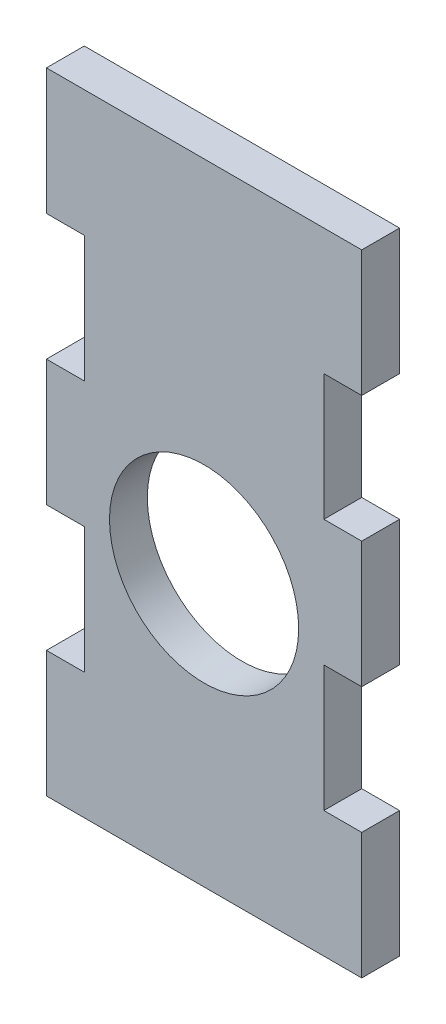
SolidWorks part; units mm, degrees
material "PC High Viscosity"
ref_plane "Front Plane" through (0, 0, 0) normal (0, 0, 1) x (1, 0, 0)
ref_plane "Top Plane" through (0, 0, 0) normal (0, 1, 0) x (1, 0, 0)
ref_plane "Right Plane" through (0, 0, 0) normal (1, 0, 0) x (0, 0, -1)
sketch "Sketch1" plane through (0, 0, 0) normal (0, 0, 1) x (1, 0, 0)
  line L1 (12.5, -25) -> (-12.5, -25)
  line L2 (12.5, -25) -> (12.5, 25)
  line L3 (12.5, 25) -> (-12.5, 25)
  line L4 (-12.5, -25) -> (-12.5, 25)
  line L5 (12.5, -25) -> (-12.5, 25) construction
  line L6 (12.5, 25) -> (-12.5, -25) construction
  point P0 (0, 0)
  dimension "D1" = 25
  dimension "D2" = 50
extrude "Boss-Extrude1" add sketch "Sketch1" along normal blind 3
sketch "Sketch2" plane through (0, 0, 3) normal (0, 0, 1) x (1, 0, 0)
  line L0 (12.5, -25) -> (12.5, 25) construction
  line L1 (12.5, 15) -> (9.5, 15)
  line L2 (12.5, 15) -> (12.5, 5)
  line L3 (12.5, 5) -> (9.5, 5)
  line L4 (9.5, 15) -> (9.5, 5)
  line L5 (0, 25) -> (0, -25) construction
  line L6 (12.5, -5) -> (9.5, -5)
  line L7 (12.5, -5) -> (12.5, -15)
  line L8 (12.5, -15) -> (9.5, -15)
  line L9 (9.5, -5) -> (9.5, -15)
  line L10 (12.5, 25) -> (-12.5, 25) construction
  line L11 (-12.5, -25) -> (12.5, -25) construction
  line L12 (12.5, 0) -> (-12.5, 0) construction
  line L13 (-12.5, 25) -> (-12.5, -25) construction
  line L14 (12.5, 5) -> (12.5, -5) construction
  line L15 (-9.5, -5) -> (-9.5, -15)
  line L16 (-12.5, -15) -> (-9.5, -15)
  line L17 (-12.5, -5) -> (-12.5, -15)
  line L18 (-12.5, -5) -> (-9.5, -5)
  line L19 (-9.5, 15) -> (-9.5, 5)
  line L20 (-12.5, 5) -> (-9.5, 5)
  line L21 (-12.5, 15) -> (-12.5, 5)
  line L22 (-9.5, 15) -> (-12.5, 15)
  line L23 (-12.5, 25) -> (0, 25) construction
  line L24 (-12.5, 25) -> (-12.5, 12.5) construction
  line L25 (-12.5, 12.5) -> (0, 12.5) construction
  line L26 (0, 25) -> (0, 12.5) construction
  circle A0 centre (0, -3.5) radius 7.5
  dimension "D4" = 15
  dimension "D1" = 10
  dimension "D2" = 3
  dimension "D3" = 16
extrude "Cut-Extrude1" cut sketch "Sketch2" against normal through all
equation "\"pulley_pitch_diam\"= 12.73mm"
equation "\"pulley_total_width\"= 16mm"
equation "\"pulley_total_diam\"= 16mm"
equation "\"belt_width\"= 6mm"
equation "\"material_thickness\"= 3mm"
equation "\"shaft_diam\"= 8mm"
equation "\"bearing_od\"= 22mm"
equation "\"bearing_thickness\"= 7mm"
equation "\"D1@Boss-Extrude1\"=\"material_thickness\""
equation "\"D2@Sketch2\"=\"material_thickness\""
